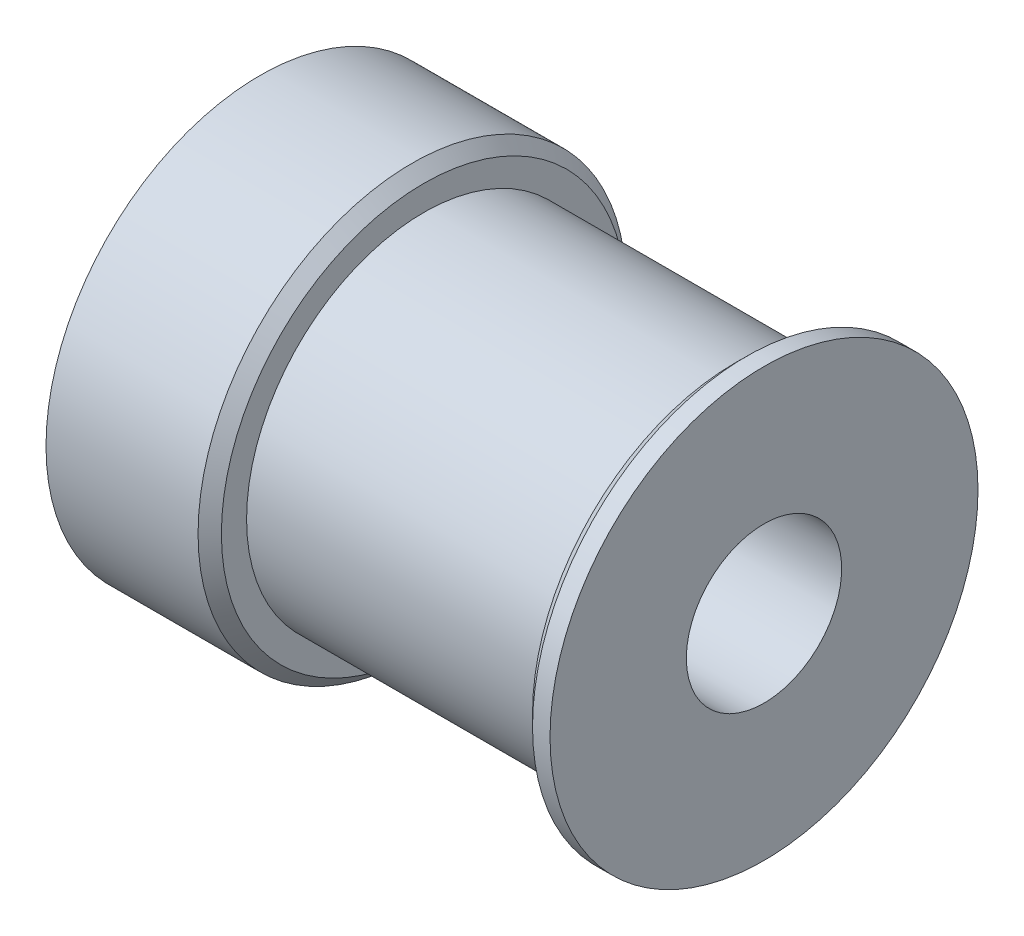
SolidWorks part; units mm, degrees
ref_plane "Front Plane" through (0, 0, 0) normal (0, 0, 1) x (1, 0, 0)
ref_plane "Top Plane" through (0, 0, 0) normal (0, 1, 0) x (1, 0, 0)
ref_plane "Right Plane" through (0, 0, 0) normal (1, 0, 0) x (0, 0, -1)
sketch "Sketch1" plane through (0, 0, 0) normal (0, 0, 1) x (1, 0, 0)
  line L0 (0, 0) -> (4503.6671, 0) construction
  line L2 (-10.5864, 3.995) -> (-7.4649, 3.995)
  line L3 (-10.5864, 3.995) -> (-10.5864, 11.005)
  line L4 (-10.5864, 11.005) -> (-2.1664, 11.005)
  line L5 (-2.1664, 9.11) -> (-2.1664, 11.005)
  line L6 (-7.4649, 3.995) -> (-1.4317, 3.995)
  line L8 (-2.1664, 9.11) -> (13.8336, 9.11)
  line L10 (-1.4317, 3.995) -> (15.3336, 3.995)
  line L11 (13.8336, 9.11) -> (13.8336, 11.005)
  line L12 (13.8336, 11.005) -> (15.3336, 11.005)
  line L13 (15.3336, 3.995) -> (15.3336, 11.005)
  dimension "D1" = 18.22
  dimension "D2" = 22.01
  dimension "D3" = 1.5
  dimension "D4" = 8.42
  dimension "D5" = 16
  dimension "D6" = 7.99
  dimension "D7" = 10.5864
revolve "Revolve1" add sketch "Sketch1" angle 360 about L0
sketch "Sketch2" plane through (0, 0, 0) normal (0, 0, 1) x (1, 0, 0)
  line L0 (0, 0) -> (-10.5864, 0) construction
  line L1 (-10.5864, 11.005) -> (-10.5864, -11.005) construction
  line L2 (-6.3764, 11.005) -> (-6.3764, 0) construction
  line L3 (-2.1664, 11.005) -> (-10.5864, 11.005) construction
  circle A0 centre (-6.3764, 0) radius 1.75
  dimension "D1" = 3.5
extrude "Cut-Extrude1" cut sketch "Sketch2" against normal blind 17
pattern_circular "CirPattern1" count 2 over 90 about axis through (-10.5864, 0, 0) along (-1, 0, 0) of "Cut-Extrude1"
chamfer "Chamfer1" distance 0.6 angle 45 2 edges at (13.8336, 0, 11.005) (-2.1664, 0, 11.005)
